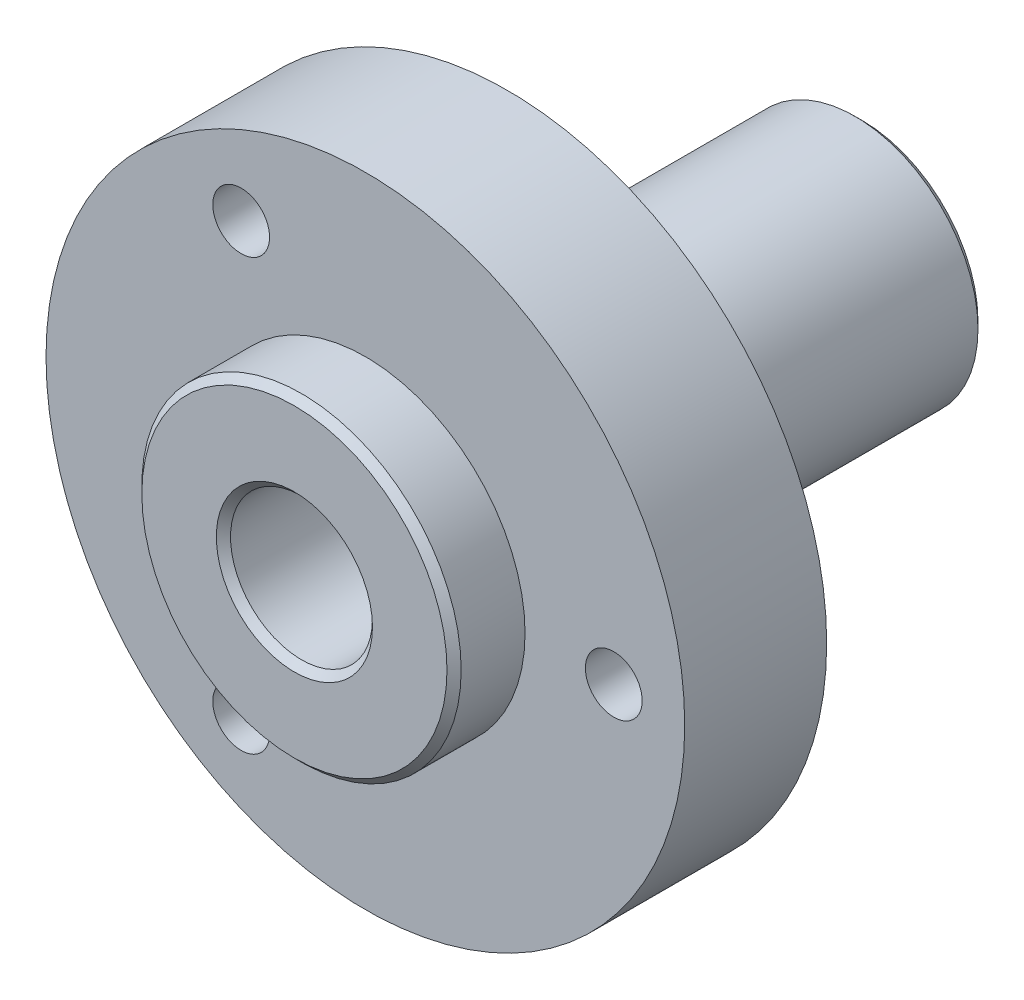
SolidWorks part; units mm, degrees
ref_plane "Front Plane" through (0, 0, 0) normal (0, 0, 1) x (1, 0, 0)
ref_plane "Top Plane" through (0, 0, 0) normal (0, 1, 0) x (1, 0, 0)
ref_plane "Right Plane" through (0, 0, 0) normal (1, 0, 0) x (0, 0, -1)
sketch "Sketch1" plane through (0, 0, 0) normal (0, 0, 1) x (1, 0, 0)
  circle A0 centre (0, 0) radius 4.5 construction
  circle A1 centre (0, 0) radius 4.5
extrude "Boss-Extrude1" add sketch "Sketch1" against normal up to vertex (2 mm away)
sketch "Sketch2" plane through (0, 0, -2) normal (0, 0, -1) x (-1, 0, 0)
  circle A0 centre (0, 0) radius 9 construction
  circle A1 centre (0, 0) radius 9
extrude "Boss-Extrude2" add sketch "Sketch2" along normal blind 4
sketch "Sketch3" plane through (0, 0, -6) normal (0, 0, -1) x (-1, 0, 0)
  circle A0 centre (0, 0) radius 3.4638
extrude "Boss-Extrude3" add sketch "Sketch3" along normal blind 10
hole_wizard "M2x0.4 Tapped Hole1" positions "Sketch4" profile "Sketch5" tap size "M2x0.4" standard "ANSI Metric" end condition through all
sketch "Sketch4" plane through (0, 0, -2) normal (0, 0, 1) x (1, 0, 0)
  point P0 (-3.5, 6.0622)
  point P3 (-3.5, -6.0622)
  point P6 (7, 0)
sketch "Sketch5" plane through (-3.5, 6.0622, -2) normal (1, 0, 0) x (0, -1, 0)
  line L0 (0, 0) -> (0, 14)
  line L1 (0, 14) -> (0.8, 14)
  line L2 (0.8, 14) -> (0.8, 0)
  line L5 (0.8, 0) -> (0, 0)
  line L11 (0, -6.35) -> (0, 107.95) construction
  dimension "Thru Tap Drill Dia." = 1.6
  dimension "Thru Tap Drill Depth" = 14
cosmetic thread "Hole Thread1" parameters "D2"=2
cosmetic thread "Hole Thread2" parameters "D2"=2
cosmetic thread "Hole Thread3" parameters "D2"=2
sketch "Sketch7" plane through (0, 0, 0) normal (0, 0, 1) x (1, 0, 0)
  circle A0 centre (0, 0) radius 2 construction
  circle A1 centre (0, 0) radius 2
extrude "Cut-Extrude3" cut sketch "Sketch7" against normal through all
chamfer "Chamfer1" distance 0.2 angle 45 4 edges at (-3.4638, 0, -16) (2, 0, -16) (4.5, 0, 0) (2, 0, 0)
